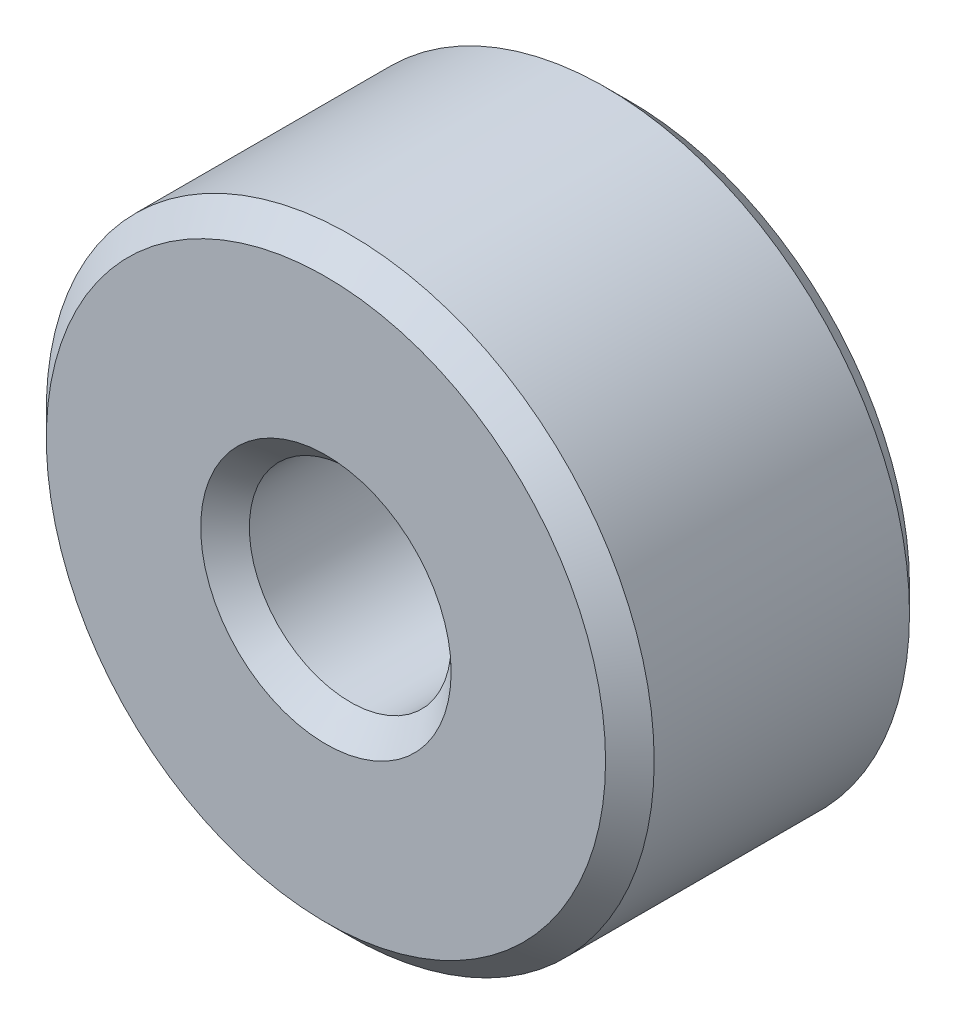
SolidWorks part; units mm, degrees
ref_plane "Front Plane" through (0, 0, 0) normal (0, 0, 1) x (1, 0, 0)
ref_plane "Top Plane" through (0, 0, 0) normal (0, 1, 0) x (1, 0, 0)
ref_plane "Right Plane" through (0, 0, 0) normal (1, 0, 0) x (0, 0, -1)
sketch "Sketch1" plane through (0, 0, 0) normal (0, 0, 1) x (1, 0, 0)
  circle A0 centre (0, 0) radius 6.35
  circle A1 centre (0, 0) radius 2.1082
  dimension "OD" = 12.7
  dimension "ID" = 4.2164
sketch "Sketch2" plane through (0, 0, 0) normal (1, 0, 0) x (0, 0, -1)
  line L0 (-3.175, 0) -> (3.175, 0) construction
  point P0 (3.175, 6.35)
  point P3 (0, 0)
  point P6 (-3.175, 6.35)
  point P7 (0, 6.35)
  dimension "Length" = 6.35
sketch "Sketch3" plane through (0, 0, 0) normal (0, 0, 1) x (1, 0, 0)
  circle A0 centre (0, 0) radius 6.35 construction
  circle A1 centre (0, 0) radius 2.1082 construction
  circle A2 centre (0, 0) radius 6.35
  circle A3 centre (0, 0) radius 2.1082
extrude "Boss-Extrude1" add sketch "Sketch3" against normal up to vertex (3.175 mm away) and the other way up to vertex (3.175 mm away) up to point (0, 0, -3.175) other way up to point (0, 0, 3.175)
chamfer "Chamfer1" distance 0.508 angle 45 4 edges at (6.35, 0, 3.175) (6.35, 0, -3.175) (2.1082, 0, -3.175) (2.1082, 0, 3.175)
sketch "Sketch4" plane through (0, 0, 0) normal (1, 0, 0) x (0, 0, -1)
  line L0 (2.667, 2.1082) -> (-2.667, 2.1082)
  line L1 (-2.667, -2.1082) -> (2.667, -2.1082)
  line L2 (-2.667, -2.1082) -> (2.667, -2.1082)
  line L3 (2.667, 2.1082) -> (-2.667, 2.1082)
